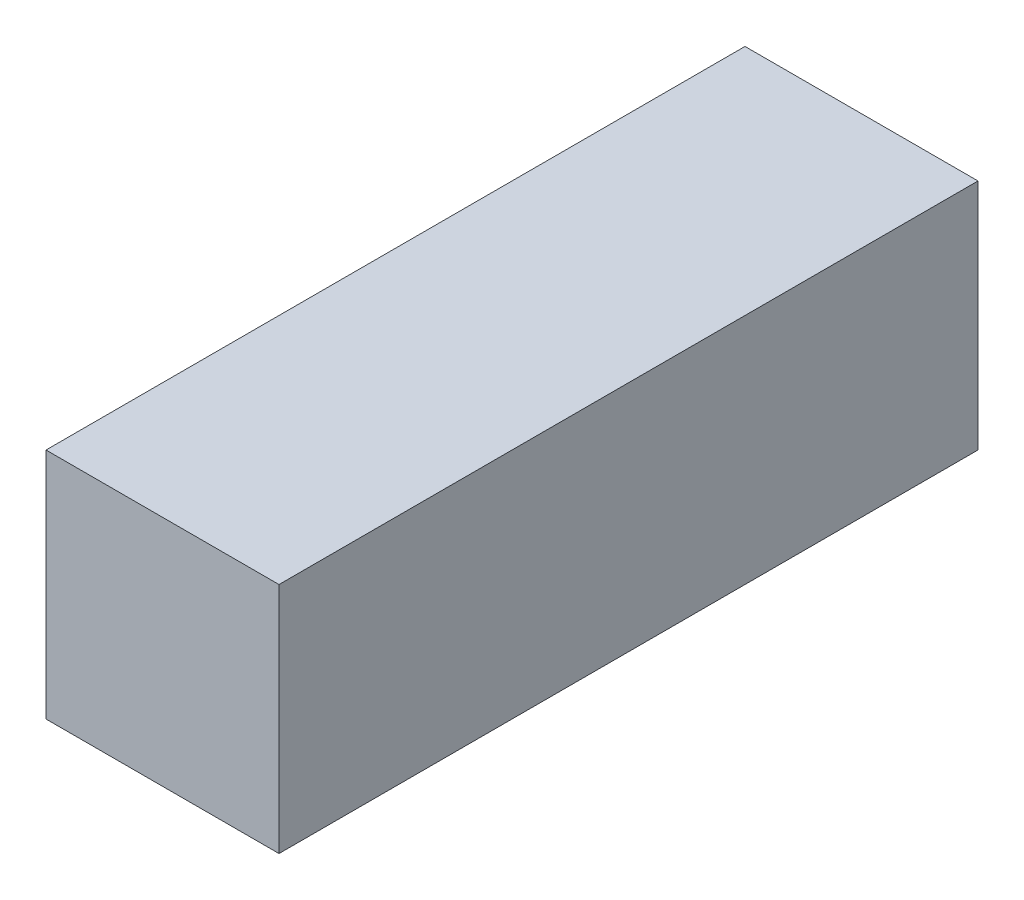
SolidWorks part; units mm, degrees
ref_plane "Front Plane" through (0, 0, 0) normal (0, 0, 1) x (1, 0, 0)
ref_plane "Top Plane" through (0, 0, 0) normal (0, 1, 0) x (1, 0, 0)
ref_plane "Right Plane" through (0, 0, 0) normal (1, 0, 0) x (0, 0, -1)
sketch "Sketch1" plane through (0, 0, 0) normal (0, 1, 0) x (1, 0, 0)
  line L1 (-57.5042, 559.0381) -> (142.4958, 559.0381)
  line L2 (-57.5042, 559.0381) -> (-57.5042, -40.9619)
  line L3 (-57.5042, -40.9619) -> (142.4958, -40.9619)
  line L4 (142.4958, 559.0381) -> (142.4958, -40.9619)
  dimension "D1" = 200
  dimension "D2" = 600
extrude "Boss-Extrude1" add sketch "Sketch1" along normal blind 200
